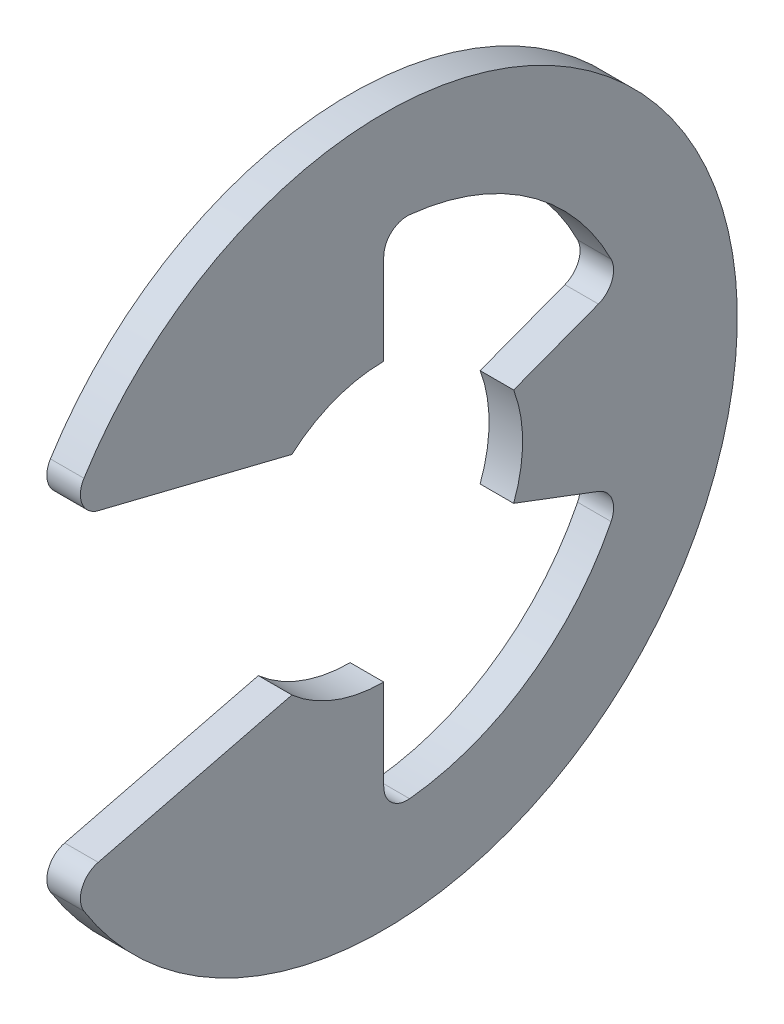
SolidWorks part; units mm, degrees
ref_plane "Front" through (0, 0, 0) normal (0, 0, 1) x (1, 0, 0)
ref_plane "Top" through (0, 0, 0) normal (0, 1, 0) x (1, 0, 0)
ref_plane "Right" through (0, 0, 0) normal (1, 0, 0) x (0, 0, -1)
sketch "Sketch1" plane through (0, 0, 0) normal (1, 0, 0) x (0, 0, -1)
  line L0 (-5.9715, -3.0225) -> (-1.7389, -1.9717)
  line L1 (-5.9715, 3.0225) -> (-1.7389, 1.9717)
  line L2 (0, -2.6289) -> (0, -4.8113)
  line L3 (0, 2.6289) -> (0, 4.8113)
  line L4 (2.4591, -0.9295) -> (4.5005, -1.701)
  line L5 (2.4591, 0.9295) -> (4.5005, 1.701)
  line L6 (0, 0) -> (-6.858, 0) construction
  line L7 (2.4591, 0.9295) -> (2.4591, -0.9295) construction
  line L8 (0, -2.6289) -> (-1.7389, -1.9717) construction
  line L9 (0, 6.6929) -> (0, -6.6929) construction
  circle A1 centre (0, 0) radius 6.858 construction
  circle A2 centre (0, 0) radius 2.6289 construction
  arc A3 (-5.9715, -3.0225) -> (-5.9715, 3.0225) centre (0, 0) ccw
  arc A4 (-1.7389, -1.9717) -> (0, -2.6289) centre (0, 0) ccw
  arc A5 (-1.7389, 1.9717) -> (0, 2.6289) centre (0, 0) cw
  arc A6 (2.4591, 0.9295) -> (2.4591, -0.9295) centre (0, 0) cw
  arc A7 (0, -4.8113) -> (4.5005, -1.701) centre (0, 0) ccw
  arc A8 (4.5005, 1.701) -> (0, 4.8113) centre (0, 0) ccw
  dimension "D" = 5.2578
  dimension "D1" = 4.8113
  dimension "OD" = 13.3858
  dimension "D2" = 2.9892
  dimension "D3" = 3.9434
extrude "Extrude1" add sketch "Sketch1" along normal mid plane 0.635
fillet "Fillet1" radius 0.4445 6 edges at (0, -4.8113, 0) (0, 4.8113, 0) (0, -3.0225, 5.9715) (0, 3.0225, 5.9715) (0, -1.701, -4.5005) (0, 1.701, -4.5005)
sketch "Sketch3" plane through (0, 0, 0) normal (0, 1, 0) x (1, 0, 0)
  line L0 (0.3683, 3.175) -> (0.3683, 2.667)
  line L1 (0.3683, 2.667) -> (-0.3683, 2.667)
  line L2 (-0.3683, 2.667) -> (-0.3683, 3.175)
  line L3 (-0.3683, 3.175) -> (-7.9185, 3.175)
  line L4 (3.1306, 0) -> (3.1306, 2.921)
  line L5 (-7.9185, 3.175) -> (-7.9185, 0)
  line L6 (-7.9185, 0) -> (3.1306, 0)
  line L8 (3.1306, 0) -> (3.1306, 3.175) construction
  line L9 (3.1306, 3.175) -> (0.3683, 3.175) construction
  line L10 (3.1306, 0) -> (17.2631, 0) construction
  line L11 (3.1306, 2.921) -> (2.8765, 3.175)
  line L12 (2.8765, 3.175) -> (0.3683, 3.175)
  point P2 (0, 2.667)
  point P5 (0.3683, 2.921)
  dimension "D2" = 11.049
  dimension "D1" = 2.7622
  dimension "D3" = 45
revolve "Revolve2" [suppressed] add sketch "Sketch3" angle 360 about L10
equation "\"D2@Sketch3\" = \"W@Sketch3\"*15"
equation "\"D1@Sketch3\" = \"D2@Sketch3\"/4"
equation "\"D1@Sketch1\" = (\"OD@Sketch1\"+\"D@Sketch1\")/3.875"
equation "\"D3@Sketch1\" = \"D@Sketch1\"*.75"
equation "\"D1@Fillet1\" = \"D1@Extrude1\"*.7"
